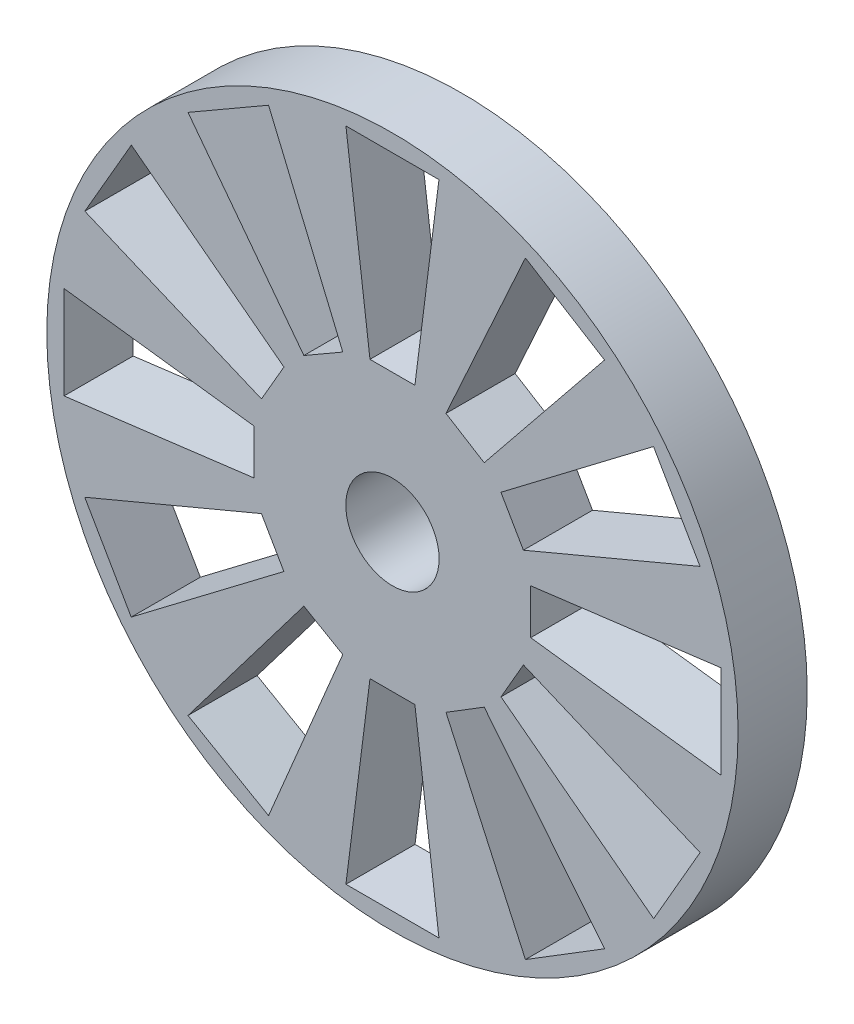
SolidWorks part; units mm, degrees
ref_plane "Plano frontal" through (0, 0, 0) normal (0, 0, 1) x (1, 0, 0)
ref_plane "Plano superior" through (0, 0, 0) normal (0, 1, 0) x (1, 0, 0)
ref_plane "Plano direito" through (0, 0, 0) normal (1, 0, 0) x (0, 0, -1)
sketch "Esboço1" plane through (0, 0, 0) normal (0, 0, 1) x (1, 0, 0)
  line L0 (-1.3455, 9.5) -> (1.3455, 9.5)
  line L3 (0, 4) -> (0.65, 4)
  line L4 (0, 4) -> (-0.65, 4)
  line L6 (0.65, 4) -> (1.3455, 9.5)
  line L7 (-0.65, 4) -> (-1.3455, 9.5)
  line L9 (2.655, 3.0616) -> (6.137, 7.3755)
  line L10 (2.102, 3.4032) -> (2.655, 3.0616)
  line L11 (2.102, 3.4032) -> (1.549, 3.7447)
  line L45 (1.549, 3.7447) -> (3.8476, 8.7896)
  line L51 (6.137, 7.3755) -> (3.8476, 8.7896)
  line L58 (-1.4367, 3.7893) -> (-3.5838, 8.9004)
  line L59 (-1.9996, 3.4643) -> (-1.4367, 3.7893)
  line L65 (-1.9996, 3.4643) -> (-2.5626, 3.1394)
  line L71 (-2.5626, 3.1394) -> (-5.9143, 7.5552)
  line L72 (-3.5838, 8.9004) -> (-5.9143, 7.5552)
  line L79 (-3.4636, 2.0008) -> (-3.7888, 1.4379)
  line L85 (-3.4636, 2.0008) -> (-3.1385, 2.5636)
  line L86 (-3.1385, 2.5636) -> (-7.5532, 5.9169)
  line L87 (-8.8992, 3.5868) -> (-7.5532, 5.9169)
  line L88 (-3.7888, 1.4379) -> (-8.8992, 3.5868)
  line L90 (-4, 0.0014) -> (-4.0002, -0.6486)
  line L91 (-4.0002, -0.6486) -> (-9.5005, -1.3422)
  line L92 (-9.4995, 1.3487) -> (-9.5005, -1.3422)
  line L93 (-3.9998, 0.6514) -> (-9.4995, 1.3487)
  line L94 (-4, 0.0014) -> (-3.9998, 0.6514)
  line L96 (-3.465, -1.9984) -> (-3.1403, -2.5615)
  line L97 (-3.1403, -2.5615) -> (-7.5572, -5.9118)
  line L98 (-7.5572, -5.9118) -> (-8.9016, -3.5807)
  line L99 (-3.7898, -1.4354) -> (-8.9016, -3.5807)
  line L100 (-3.465, -1.9984) -> (-3.7898, -1.4354)
  line L103 (-1.9996, -3.4643) -> (-1.4367, -3.7893)
  line L104 (-1.9996, -3.4643) -> (-2.5626, -3.1394)
  line L105 (-2.5626, -3.1394) -> (-5.9143, -7.5552)
  line L106 (-3.5838, -8.9004) -> (-5.9143, -7.5552)
  line L107 (-1.4367, -3.7893) -> (-3.5838, -8.9004)
  line L108 (-0.65, -4) -> (-1.3455, -9.5)
  line L109 (0, -4) -> (-0.65, -4)
  line L110 (0, -4) -> (0.65, -4)
  line L111 (0.65, -4) -> (1.3455, -9.5)
  line L112 (-1.3455, -9.5) -> (1.3455, -9.5)
  line L113 (2.102, -3.4032) -> (2.655, -3.0616)
  line L114 (2.102, -3.4032) -> (1.549, -3.7447)
  line L115 (1.549, -3.7447) -> (3.8476, -8.7896)
  line L116 (6.137, -7.3755) -> (3.8476, -8.7896)
  line L117 (2.655, -3.0616) -> (6.137, -7.3755)
  line L119 (3.465, -1.9984) -> (3.7898, -1.4354)
  line L120 (3.7898, -1.4354) -> (8.9016, -3.5807)
  line L121 (7.5572, -5.9118) -> (8.9016, -3.5807)
  line L122 (3.1403, -2.5615) -> (7.5572, -5.9118)
  line L123 (3.465, -1.9984) -> (3.1403, -2.5615)
  line L124 (4, 0.0014) -> (3.9998, 0.6514)
  line L125 (3.9998, 0.6514) -> (9.4995, 1.3487)
  line L126 (9.4995, 1.3487) -> (9.5005, -1.3422)
  line L127 (4.0002, -0.6486) -> (9.5005, -1.3422)
  line L128 (4, 0.0014) -> (4.0002, -0.6486)
  line L129 (3.4636, 2.0008) -> (3.1385, 2.5636)
  line L130 (3.1385, 2.5636) -> (7.5532, 5.9169)
  line L131 (8.8992, 3.5868) -> (7.5532, 5.9169)
  line L132 (3.7888, 1.4379) -> (8.8992, 3.5868)
  line L133 (3.4636, 2.0008) -> (3.7888, 1.4379)
  circle A0 centre (0, 0) radius 10
  circle A1 centre (0, 0) radius 1.35
  dimension "D1" = 20
  dimension "D2" = 2.7
  dimension "D7" = 0.65
extrude "Ressalto-extrusão2" add sketch "Esboço1" along normal blind 2
